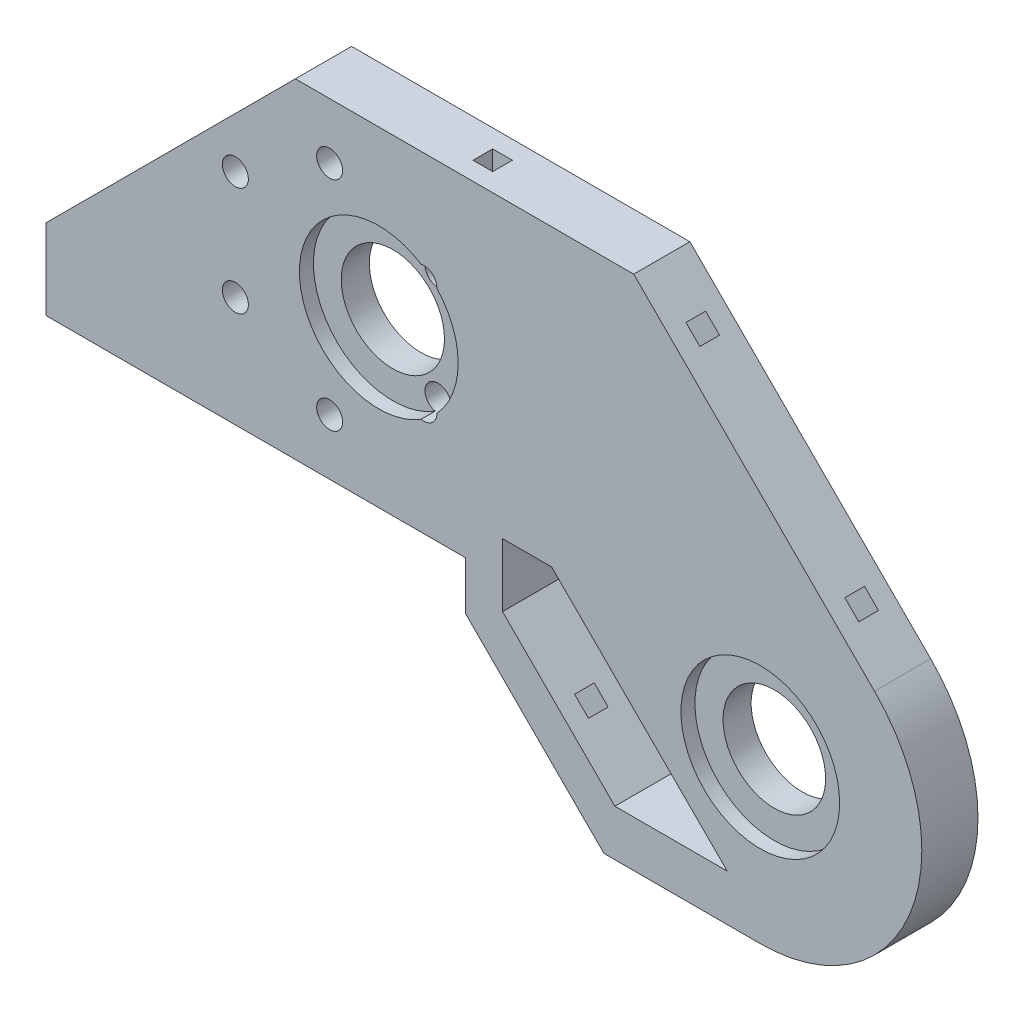
SolidWorks part; units mm, degrees
ref_plane "Plano frontal" through (0, 0, 0) normal (0, 0, 1) x (1, 0, 0)
ref_plane "Plano superior" through (0, 0, 0) normal (0, 1, 0) x (1, 0, 0)
ref_plane "Plano direito" through (0, 0, 0) normal (1, 0, 0) x (0, 0, -1)
sketch "Model" plane through (0, 0, 0) normal (0, 0, 1) x (1, 0, 0)
  line L0 (0, 0) -> (39, 0)
  line L1 (39, 0) -> (39.7, 0)
  line L2 (39.7, 0) -> (39.7, -6.8548)
  line L3 (0, 0) -> (0, 31.4419)
  line L4 (50.1111, 46.949) -> (15.5071, 46.949)
  line L5 (0, 31.4419) -> (15.5071, 46.949)
  line L6 (39.7, -6.8548) -> (52.4452, -19.6)
  line L7 (72, -15) -> (52, 5)
  line L8 (97.9635, 12.6635) -> (63.6779, 46.949)
  line L9 (50.1111, 46.949) -> (63.6779, 46.949)
  line L10 (52.4452, -19.6) -> (59.4452, -26.6)
  line L11 (81.7, -26.6) -> (59.4452, -26.6)
  line L12 (72, -15) -> (77, -20)
  line L13 (52, 5) -> (45, 5)
  line L14 (45, 5) -> (45, -4)
  line L15 (45, -4) -> (61, -20)
  line L16 (61, -20) -> (77, -20)
  circle A2 centre (59.0726, 19.0274) radius 7.35
  arc A5 (81.7, -26.6) -> (97.9635, 12.6635) centre (81.7, -3.6) ccw
  circle A6 centre (81.7, -3.6) radius 7.3
  circle A7 centre (6.9606, 15.731) radius 1.85
  circle A8 centre (6.9606, 31.231) radius 1.85
  circle A9 centre (20.384, 38.981) radius 1.85
  circle A10 centre (33.8074, 31.231) radius 1.85
  circle A11 centre (33.8074, 15.731) radius 1.85
  circle A12 centre (20.384, 7.981) radius 1.85
  circle A13 centre (27.384, 23.481) radius 7.35
sketch "Esboço2" plane through (0, 0, 0) normal (0, 0, 1) x (1, 0, 0)
  circle A15 centre (6.9606, 15.731) radius 3.3
  circle A16 centre (6.9606, 31.231) radius 3.3
  circle A17 centre (33.8074, 15.731) radius 3.3
  circle A18 centre (20.384, 38.981) radius 3.3
  circle A19 centre (33.8074, 31.231) radius 3.3
  circle A20 centre (20.384, 7.981) radius 3.3
sketch "Esboço3" plane through (0, 0, 0) normal (0, 0, 1) x (1, 0, 0)
  circle A3 centre (81.7, -3.6) radius 11.3
  circle A4 centre (59.0726, 19.0274) radius 11.3
  circle A14 centre (27.384, 23.481) radius 11.3
extrude "Ressalto-extrusão1" add sketch "Model" along normal blind 8
sketch "Esboço4" plane through (0, 0, 8) normal (0, 0, 1) x (1, 0, 0)
  circle A3 centre (81.7, -3.6) radius 11.3
  circle A4 centre (59.0726, 19.0274) radius 11.3
  circle A14 centre (27.384, 23.481) radius 11.3
extrude "Corte-extrusão1" cut sketch "Esboço3" along normal blind 2
extrude "Corte-extrusão2" cut sketch "Esboço4" against normal blind 2
extrude "Corte-extrusão4" cut sketch "Esboço2" along normal blind 2
sketch "Esboço7" plane through (55.3135, 55.3135, 0) normal (0.7071, 0.7071, 0) x (0, 0, -1)
  line L0 (0, -36.0727) -> (-8, -36.0727) construction
  line L2 (-4, -52.0727) -> (-4, -20.0727) construction
  line L3 (-5.4, -50.6727) -> (-2.6, -50.6727)
  line L4 (-5.4, -18.6727) -> (-2.6, -18.6727)
  line L5 (-5.4, -18.6727) -> (-5.4, -21.4727)
  line L6 (-5.4, -21.4727) -> (-2.6, -21.4727)
  line L7 (-2.6, -18.6727) -> (-2.6, -21.4727)
  line L8 (-5.4, -18.6727) -> (-2.6, -21.4727) construction
  line L9 (-5.4, -21.4727) -> (-2.6, -18.6727) construction
  line L10 (-2.6, -50.6727) -> (-2.6, -53.4727)
  line L11 (-5.4, -50.6727) -> (-2.6, -53.4727) construction
  line L12 (-5.4, -53.4727) -> (-2.6, -53.4727)
  line L13 (-5.4, -50.6727) -> (-5.4, -53.4727)
  line L14 (-5.4, -53.4727) -> (-2.6, -50.6727) construction
  line L15 (0, -60.3162) -> (0, -11.8291) construction
  line L16 (-8, -60.3162) -> (-8, -11.8291) construction
extrude "Corte-extrusão6" cut sketch "Esboço7" against normal blind 6
sketch "Esboço8" plane through (0, 46.949, 0) normal (0, 1, 0) x (1, 0, 0)
  line L0 (39.5925, 0) -> (39.5925, -8) construction
  line L1 (63.6779, 0) -> (15.5071, 0) construction
  line L2 (63.6779, -8) -> (15.5071, -8) construction
  line L4 (38.1925, -5.4) -> (40.9925, -5.4)
  line L5 (38.1925, -5.4) -> (38.1925, -2.6)
  line L6 (38.1925, -2.6) -> (40.9925, -2.6)
  line L7 (40.9925, -5.4) -> (40.9925, -2.6)
  line L8 (38.1925, -5.4) -> (40.9925, -2.6) construction
  line L9 (38.1925, -2.6) -> (40.9925, -5.4) construction
  point P6 (39.5925, -4)
extrude "Corte-extrusão7" cut sketch "Esboço8" against normal blind 6
sketch "Esboço10" plane through (16.4226, 16.4226, 0) normal (-0.7071, -0.7071, 0) x (0, 0, 1)
  line L0 (0, -46.8812) -> (8, -46.8812) construction
  line L1 (0, -32.9192) -> (0, -60.8431) construction
  line L2 (8, -32.9192) -> (8, -60.8431) construction
  line L4 (2.6, -45.4812) -> (5.4, -45.4812)
  line L5 (2.6, -45.4812) -> (2.6, -48.2812)
  line L6 (2.6, -48.2812) -> (5.4, -48.2812)
  line L7 (5.4, -45.4812) -> (5.4, -48.2812)
  line L8 (2.6, -45.4812) -> (5.4, -48.2812) construction
  line L9 (2.6, -48.2812) -> (5.4, -45.4812) construction
  point P6 (4, -46.8812)
extrude "Corte-extrusão9" cut sketch "Esboço10" against normal blind 6
sketch "Esboço13" plane through (0, 0, 8) normal (0, 0, 1) x (1, 0, 0)
  line L0 (0, 31.4419) -> (-20, 11.4419)
  line L1 (15.5071, 46.949) -> (0, 31.4419) construction
  line L2 (0, 0) -> (-20, 0)
  line L3 (0, 0) -> (-20, 0) construction
  line L4 (-20, 0) -> (-20, 11.4419)
  line L5 (0, 31.4419) -> (0, 0)
  dimension "D1" = 20
  dimension "D2" = 11.4419
extrude "Ressalto-extrusão3" add sketch "Esboço13" against normal up to surface (8 mm away) up to face at (31.6486, 23.481, 0)
sketch "Esboço6" plane through (0, 0, 0) normal (0, -1, 0) x (1, 0, 0)
  line L0 (39.7, 8) -> (39.7, 0) construction
  line L1 (4.7, 4) -> (-14.3, 4) construction
  line L2 (4.7, 4) -> (23.7, 4) construction
  circle A0 centre (4.7, 4) radius 1.5
  circle A1 centre (23.7, 4) radius 1.5
  circle A2 centre (-14.3, 4) radius 1.5
  dimension "D1" = 19
  dimension "D2" = 16
extrude "Corte-extrusão5" cut sketch "Esboço6" against normal blind 10
sketch "Esboço15" plane through (0, 0, 8) normal (0, 0, 1) x (1, 0, 0)
  circle A0 centre (59.0726, 19.0274) radius 11.3 construction
  circle A1 centre (59.0726, 19.0274) radius 11.3
extrude "Ressalto-extrusão4" add sketch "Esboço15" against normal up to surface (8 mm away) up to face at (31.6486, 23.481, 0)
sketch "Esboço14" plane through (0, 0, 8) normal (0, 0, 1) x (1, 0, 0)
  line L0 (-3.2, 8) -> (-3.2, 29.2319) construction
  line L1 (-3.2, 8) -> (-3.2, 29.2319) construction
  line L2 (-3.2, 28.2419) -> (-3.2, 0)
  line L3 (15.5071, 46.949) -> (-20, 11.4419) construction
  line L4 (-20, 0) -> (39.7, 0) construction
  line L5 (-3.2, 0) -> (-20, 0)
  line L6 (-20, 0) -> (-20, 11.4419)
  line L7 (-20, 11.4419) -> (-3.2, 28.2419)
